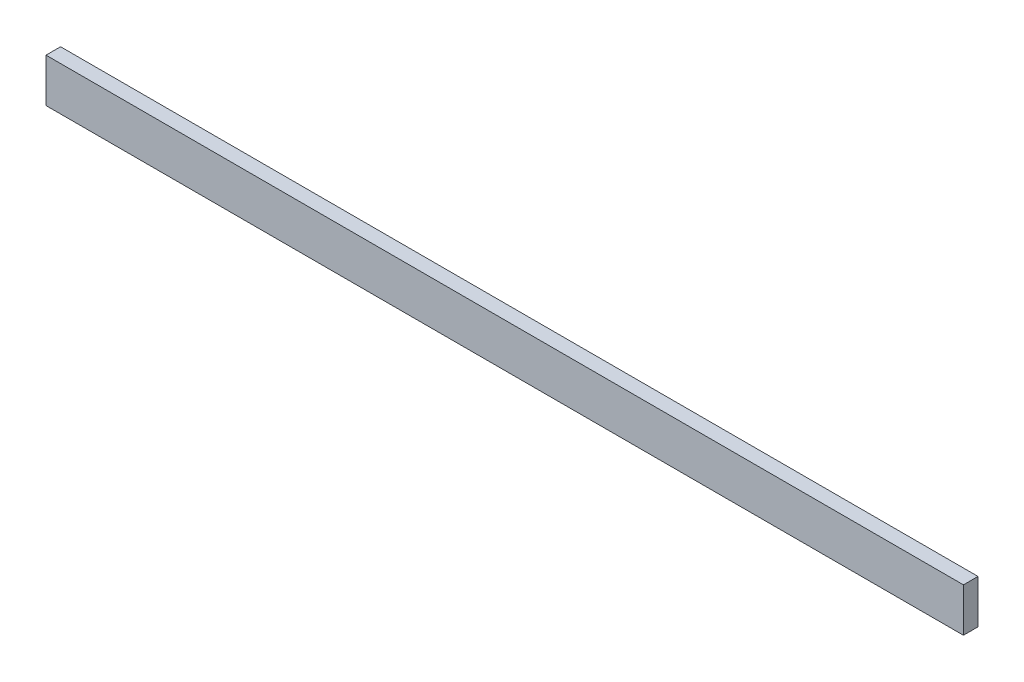
SolidWorks part; units mm, degrees
ref_plane "Front Plane" through (0, 0, 0) normal (0, 0, 1) x (1, 0, 0)
ref_plane "Top Plane" through (0, 0, 0) normal (0, 1, 0) x (1, 0, 0)
ref_plane "Right Plane" through (0, 0, 0) normal (1, 0, 0) x (0, 0, -1)
sketch "Sketch1" plane through (0, 0, 0) normal (0, 0, 1) x (1, 0, 0)
  line L1 (0, 0) -> (400.05, 0)
  line L2 (0, 0) -> (0, 19.05)
  line L3 (0, 19.05) -> (400.05, 19.05)
  line L4 (400.05, 0) -> (400.05, 19.05)
  dimension "D1" = 400.05
  dimension "D2" = 19.05
extrude "Boss-Extrude1" add sketch "Sketch1" along normal blind 6.35 contours L1 L4 L3 L2
